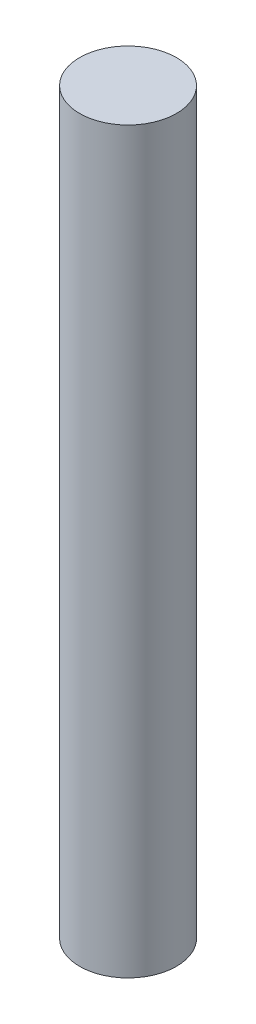
SolidWorks part; units mm, degrees
material "6061 Alloy"
ref_plane "Front Plane" through (0, 0, 0) normal (0, 0, 1) x (1, 0, 0)
ref_plane "Top Plane" through (0, 0, 0) normal (0, 1, 0) x (1, 0, 0)
ref_plane "Right Plane" through (0, 0, 0) normal (1, 0, 0) x (0, 0, -1)
sketch "Sketch1" plane through (0, 0, 0) normal (0, 0, 1) x (1, 0, 0)
  line L0 (0, 0) -> (0, 25.5113) construction
  line L1 (0, -15.25) -> (2, -15.25)
  line L2 (0, -15.25) -> (0, 15.25)
  line L3 (0, 15.25) -> (2, 15.25)
  line L4 (2, -15.25) -> (2, 15.25)
  dimension "D1" = 4
  dimension "D2" = 30.5
revolve "Revolve1" add sketch "Sketch1" angle 360 about L0
